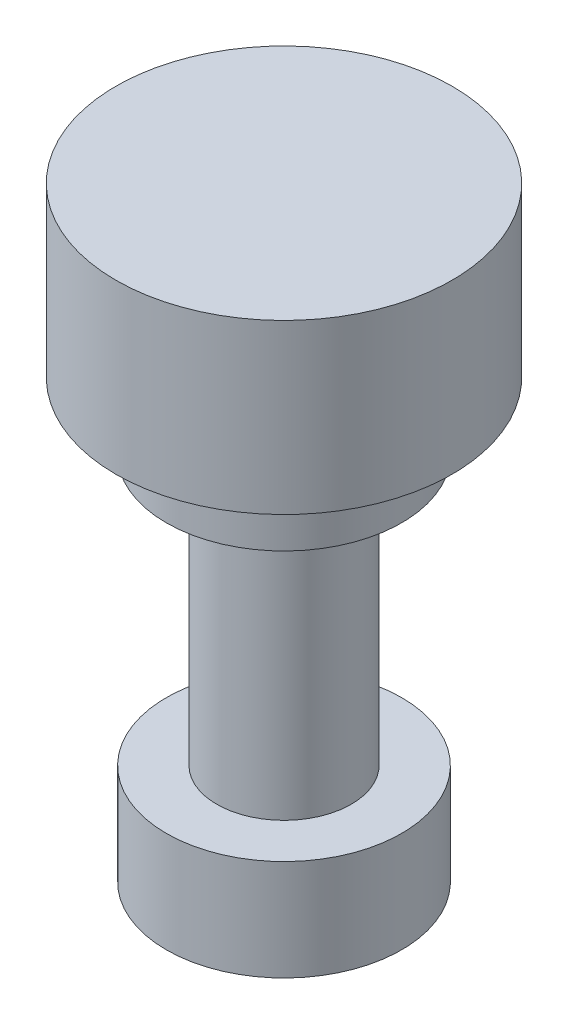
SolidWorks part; units mm, degrees
ref_plane "Front Plane" through (0, 0, 0) normal (0, 0, 1) x (1, 0, 0)
ref_plane "Top Plane" through (0, 0, 0) normal (0, 1, 0) x (1, 0, 0)
ref_plane "Right Plane" through (0, 0, 0) normal (1, 0, 0) x (0, 0, -1)
sketch "Sketch1" plane through (0, 0, 0) normal (0, 1, 0) x (1, 0, 0)
  circle A0 centre (0, 0) radius 250
  dimension "D1" = 500
extrude "Boss-Extrude1" add sketch "Sketch1" along normal mid plane 250
sketch "Sketch2" plane through (0, -125, 0) normal (0, -1, 0) x (1, 0, 0)
  circle A0 centre (0, 0) radius 175
  dimension "D1" = 350
extrude "Boss-Extrude2" add sketch "Sketch2" along normal blind 100
sketch "Sketch3" plane through (0, -225, 0) normal (0, -1, 0) x (1, 0, 0)
  circle A0 centre (0, 0) radius 100
  dimension "D1" = 200
extrude "Boss-Extrude3" add sketch "Sketch3" along normal blind 400
sketch "Sketch4" plane through (0, -625, 0) normal (0, -1, 0) x (1, 0, 0)
  circle A0 centre (0, 0) radius 175
  dimension "D1" = 350
extrude "Boss-Extrude4" add sketch "Sketch4" along normal blind 150
